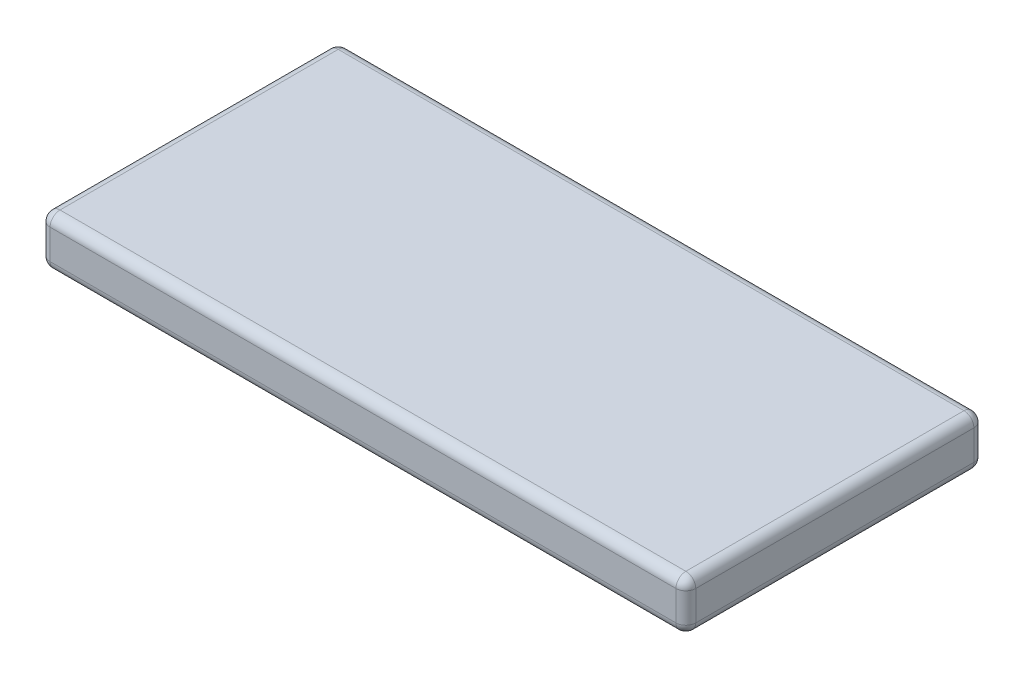
SolidWorks part; units mm, degrees
ref_plane "前视基准面" through (0, 0, 0) normal (0, 0, 1) x (1, 0, 0)
ref_plane "上视基准面" through (0, 0, 0) normal (0, 1, 0) x (1, 0, 0)
ref_plane "右视基准面" through (0, 0, 0) normal (1, 0, 0) x (0, 0, -1)
sketch "草图1" plane through (0, 0, 0) normal (0, 1, 0) x (1, 0, 0)
  line L1 (-32.5, 15) -> (32.5, 15)
  line L2 (-32.5, 15) -> (-32.5, -15)
  line L3 (-32.5, -15) -> (32.5, -15)
  line L4 (32.5, 15) -> (32.5, -15)
  line L5 (-32.5, 15) -> (32.5, -15) construction
  line L6 (-32.5, -15) -> (32.5, 15) construction
  point P0 (0, 0)
  dimension "D1" = 65
  dimension "D2" = 30
extrude "凸台-拉伸1" add sketch "草图1" along normal blind 5
fillet "圆角1" radius 1 12 edges at (-32.5, 2.5, -15) (-32.5, 0, 0) (0, 0, -15) (0, 5, -15) (32.5, 2.5, -15) (32.5, 2.5, 15) (32.5, 5, 0) (32.5, 0, 0) (0, 0, 15) (0, 5, 15) (-32.5, 2.5, 15) (-32.5, 5, 0)
